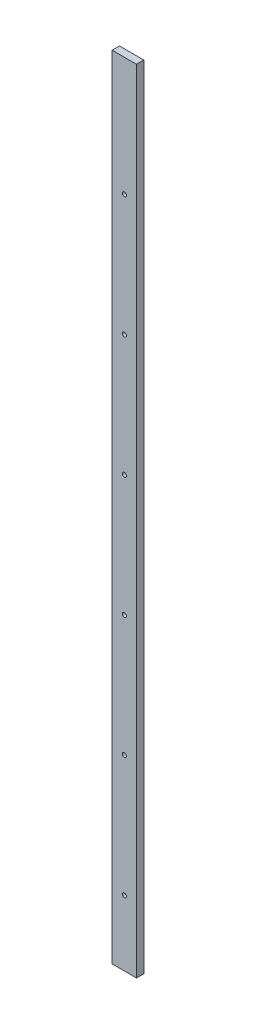
SolidWorks part; units mm, degrees
ref_plane "Front Plane" through (0, 0, 0) normal (0, 0, 1) x (1, 0, 0)
ref_plane "Top Plane" through (0, 0, 0) normal (0, 1, 0) x (1, 0, 0)
ref_plane "Right Plane" through (0, 0, 0) normal (1, 0, 0) x (0, 0, -1)
sketch "Sketch1" plane through (0, 0, 0) normal (0, 1, 0) x (1, 0, 0)
  line L1 (-20, -6) -> (20, -6)
  line L2 (-20, -6) -> (-20, 6)
  line L3 (-20, 6) -> (20, 6)
  line L4 (20, -6) -> (20, 6)
  line L5 (-20, -6) -> (20, 6) construction
  line L6 (-20, 6) -> (20, -6) construction
  point P0 (0, 0)
  dimension "D1" = 12
  dimension "D2" = 40
extrude "Boss-Extrude1" add sketch "Sketch1" against normal blind 1303.36
sketch "Sketch2" plane through (0, 0, 6) normal (0, 0, 1) x (1, 0, 0)
  line L2 (6.6, 0) -> (-6.6, 0) construction
  circle A0 centre (0, -995.5) radius 3.4
  circle A1 centre (0, -795.5) radius 3.4
  circle A2 centre (0, -395.5) radius 3.4
  circle A3 centre (0, -195.5) radius 3.4
  circle A4 centre (0, 4.5) radius 3.4
  circle A5 centre (0, -595.5) radius 3.4
  circle A6 centre (0, -1195.5) radius 3.4
  dimension "D1" = 1195.5
  dimension "D8" = 6.8
  dimension "D2" = 200
  dimension "D3" = 200
  dimension "D4" = 200
  dimension "D5" = 200
  dimension "D6" = 200
  dimension "D7" = 200
extrude "Cut-Extrude1" cut sketch "Sketch2" against normal through all
